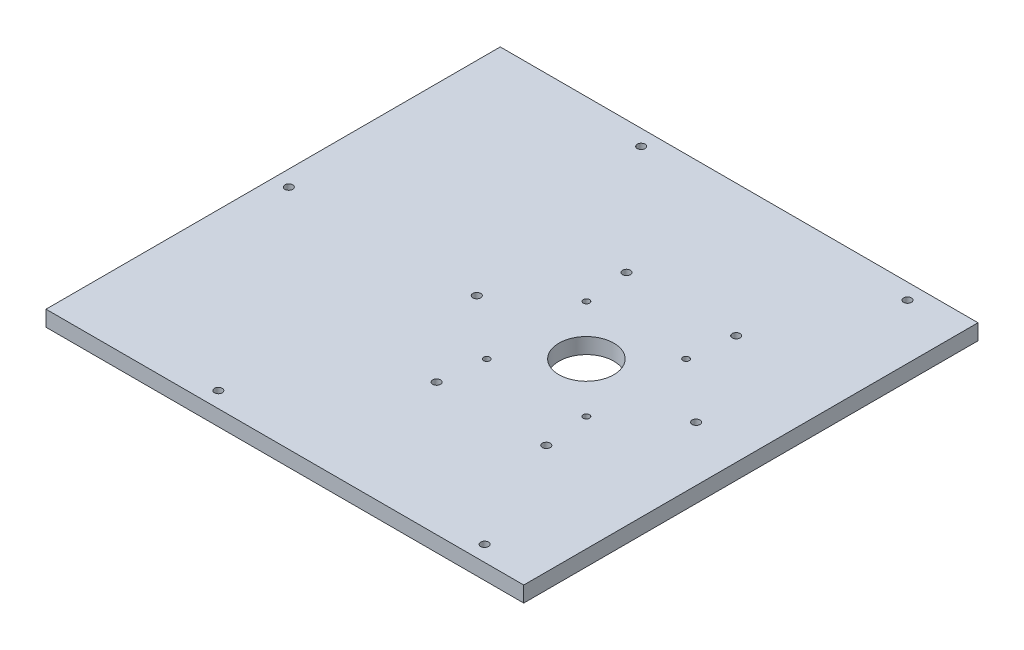
SolidWorks part; units mm, degrees
material "Acrylic (Medium-high impact)"
ref_plane "Front Plane" through (0, 0, 0) normal (0, 0, 1) x (1, 0, 0)
ref_plane "Top Plane" through (0, 0, 0) normal (0, 1, 0) x (1, 0, 0)
ref_plane "Right Plane" through (0, 0, 0) normal (1, 0, 0) x (0, 0, -1)
sketch "Sketch1" plane through (0, 0, 0) normal (0, 1, 0) x (1, 0, 0)
  line L0 (25, 0) -> (101.8483, 76.8483) construction
  line L1 (-175, 145) -> (130, 145)
  line L2 (-175, 145) -> (-175, -145)
  line L3 (-175, -145) -> (130, -145)
  line L5 (-165, 135) -> (130, 135) construction
  line L6 (-165, 135) -> (-165, -135) construction
  line L7 (-165, -135) -> (130, -135) construction
  line L9 (25, 0) -> (25, 93.5438) construction
  line L10 (130, 145) -> (130, -145)
  circle A0 centre (25, 0) radius 17.5
  circle A1 centre (25, 0) radius 45 construction
  circle A2 centre (25, 0) radius 70 construction
  circle A3 centre (95, 0) radius 2.5
  circle A4 centre (56.8198, 31.8198) radius 2
  circle A5 centre (60, -60.6218) radius 2.5
  circle A6 centre (-10, -60.6218) radius 2.5
  circle A7 centre (-45, 0) radius 2.5
  circle A8 centre (56.8198, -31.8198) radius 2
  circle A9 centre (-6.8198, -31.8198) radius 2
  circle A10 centre (-6.8198, 31.8198) radius 2
  circle A12 centre (-165, 0) radius 2.5
  circle A13 centre (-75, -135) radius 2.5
  circle A14 centre (95, -135) radius 2.5
  circle A15 centre (95, 135) radius 2.5
  circle A16 centre (-75, 135) radius 2.5
  circle A17 centre (-10, 60.6218) radius 2.5
  circle A18 centre (60, 60.6218) radius 2.5
  point P28 (25, 0)
  point P35 (25, 0)
  point P51 (25, 0)
  dimension "D10" = 35
  dimension "D12" = 140
  dimension "D13" = 90
  dimension "D14" = 5
  dimension "D16" = 4
  dimension "D20" = 5
  dimension "D21" = 5
  dimension "D22" = 5
  dimension "D23" = 5
  dimension "D24" = 5
  dimension "D1" = 290
  dimension "D3" = 175
  dimension "D4" = 145
  dimension "D5" = 10
  dimension "D6" = 10
  dimension "D8" = 10
  dimension "D11" = 145
  dimension "D15" = 45
  dimension "D26" = 145
  dimension "D18" = 4
  dimension "D17" = 6
extrude "Boss-Extrude1" add sketch "Sketch1" along normal blind 10
